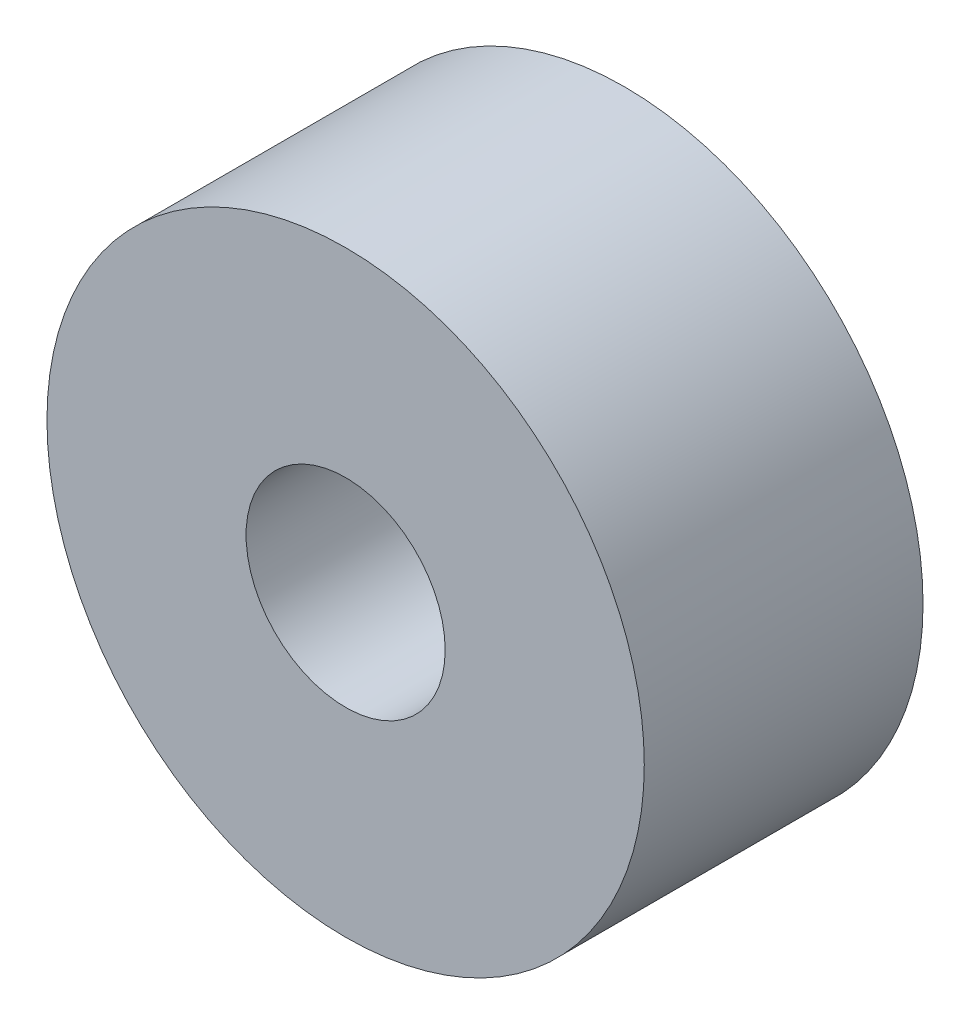
SolidWorks part; units mm, degrees
ref_plane "Front Plane" through (0, 0, 0) normal (0, 0, 1) x (1, 0, 0)
ref_plane "Top Plane" through (0, 0, 0) normal (0, 1, 0) x (1, 0, 0)
ref_plane "Right Plane" through (0, 0, 0) normal (1, 0, 0) x (0, 0, -1)
sketch "Sketch1" plane through (0, 0, 0) normal (0, 0, 1) x (1, 0, 0)
  circle A0 centre (0, 0) radius 1
  circle A1 centre (0, 0) radius 3
  dimension "D1" = 2
  dimension "D2" = 6
extrude "Boss-Extrude1" add sketch "Sketch1" along normal blind 2.8
